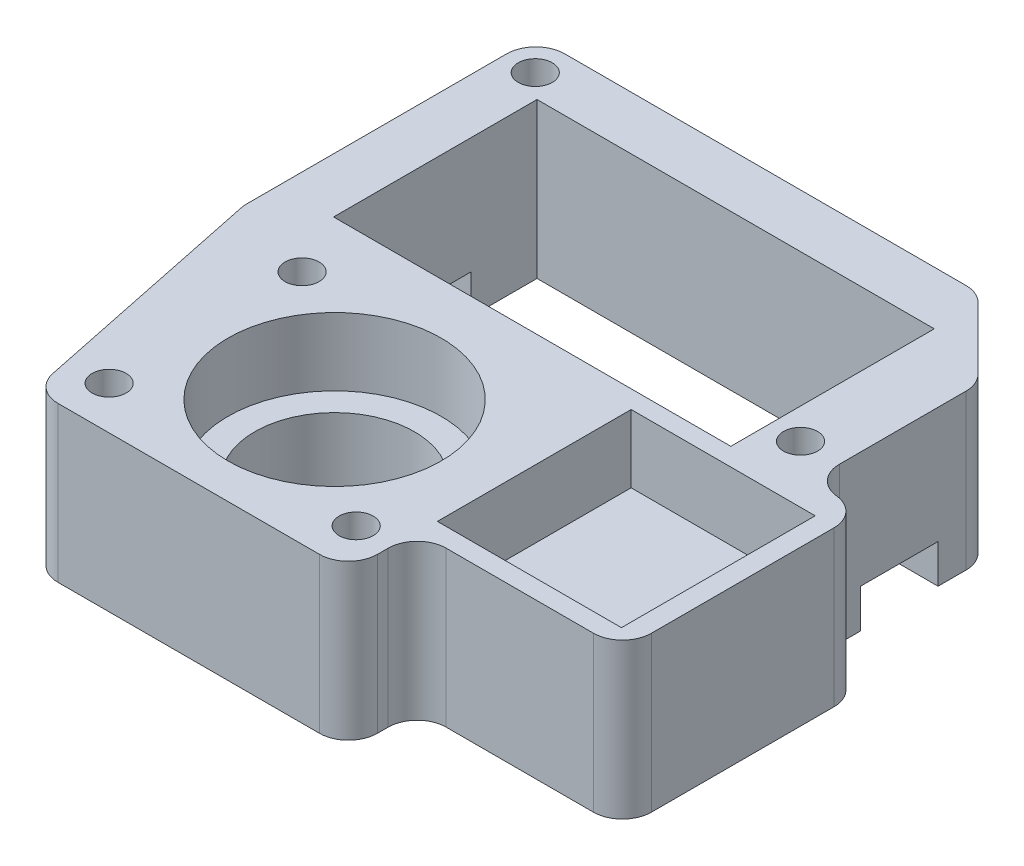
SolidWorks part; units mm, degrees
ref_plane "Plano frontal" through (0, 0, 0) normal (0, 0, 1) x (1, 0, 0)
ref_plane "Plano superior" through (0, 0, 0) normal (0, 1, 0) x (1, 0, 0)
ref_plane "Plano direito" through (0, 0, 0) normal (1, 0, 0) x (0, 0, -1)
sketch "Esboço1" plane through (0, 0, 0) normal (0, 1, 0) x (1, 0, 0)
  line L0 (-30, -1.4475) -> (-30, 28.6994)
  line L1 (8.0733, -28.6994) -> (-24.3502, -28.6994)
  line L2 (23.8541, 20.4951) -> (23.8541, 3.1856)
  line L3 (29.2611, 3.1856) -> (23.8541, 3.1856)
  line L4 (15.6498, 28.6994) -> (23.8541, 20.4951)
  line L5 (-30, 28.6994) -> (15.6498, 28.6994)
  line L6 (29.2611, 3.1856) -> (29.2611, -21.6099)
  line L7 (-30, -1.4475) -> (-24.3502, -28.6994)
  line L8 (16.6498, 2.1856) -> (-24.3502, 2.1856)
  line L9 (16.6498, 2.1856) -> (16.6498, 23.1856)
  line L10 (16.6498, 23.1856) -> (-24.3502, 23.1856)
  line L11 (-24.3502, 2.1856) -> (-24.3502, 23.1856)
  line L12 (16.6498, 2.1856) -> (-24.3502, 23.1856) construction
  line L13 (16.6498, 23.1856) -> (-24.3502, 2.1856) construction
  line L14 (8.0733, -28.6994) -> (8.0733, -21.6099)
  line L15 (29.2611, -21.6099) -> (8.0733, -21.6099)
  circle A0 centre (-7.98, -14.0802) radius 8.25
  circle A1 centre (-26.8465, 25.4987) radius 1.7594
  circle A2 centre (19.7993, 6.2334) radius 1.7594
  circle A3 centre (-21.0749, -24.2593) radius 1.7594
  circle A4 centre (4.4282, -24.2593) radius 1.7594
  circle A5 centre (-21.0749, -4.3424) radius 1.7594
  point P0 (-3.8502, 12.6856)
  point P2 (-14.3502, 13.1856)
  dimension "D1" = 41
  dimension "D2" = 21
  dimension "D3" = 10
  dimension "D4" = 28
extrude "Ressalto-extrusão1" add sketch "Esboço1" along normal blind 16
sketch "Esboço2" plane through (0, 16, 0) normal (0, 1, 0) x (1, 0, 0)
  line L1 (27.2168, -19.669) -> (8.2168, -19.669)
  line L2 (27.2168, -19.669) -> (27.2168, 0.331)
  line L3 (27.2168, 0.331) -> (8.2168, 0.331)
  line L4 (8.2168, -19.669) -> (8.2168, 0.331)
  line L5 (27.2168, -19.669) -> (8.2168, 0.331) construction
  line L6 (27.2168, 0.331) -> (8.2168, -19.669) construction
  circle A0 centre (-7.98, -14.0802) radius 11
  point P3 (17.7168, -9.669)
  dimension "D1" = 19
  dimension "D2" = 20
extrude "Corte-extrusão1" cut sketch "Esboço2" against normal blind 7
fillet "Filete2" radius 3 7 edges at (-24.3502, 8, 28.6994) (8.0733, 8, 28.6994) (-30, 8, 1.4475) (23.8541, 8, -3.1856) (23.8541, 8, -20.4951) (15.6498, 8, -28.6994) (-30, 8, -28.6994)
fillet "Filete3" radius 3 3 edges at (29.2611, 8, -3.1856) (8.0733, 8, 21.6099) (29.2611, 8, 21.6099)
sketch "Esboço4" plane through (-30, 0, 0) normal (-1, 0, 0) x (0, 0, 1)
  line L0 (-25.6994, 0) -> (1.1398, 0) construction
  line L1 (-16.3709, 0) -> (-8.3709, 0)
  line L2 (-16.3709, 0) -> (-16.3709, 4)
  line L3 (-16.3709, 4) -> (-8.3709, 4)
  line L4 (-8.3709, 0) -> (-8.3709, 4)
  dimension "D1" = 4
  dimension "D2" = 8
extrude "Corte-extrusão2" cut sketch "Esboço4" against normal blind 60
